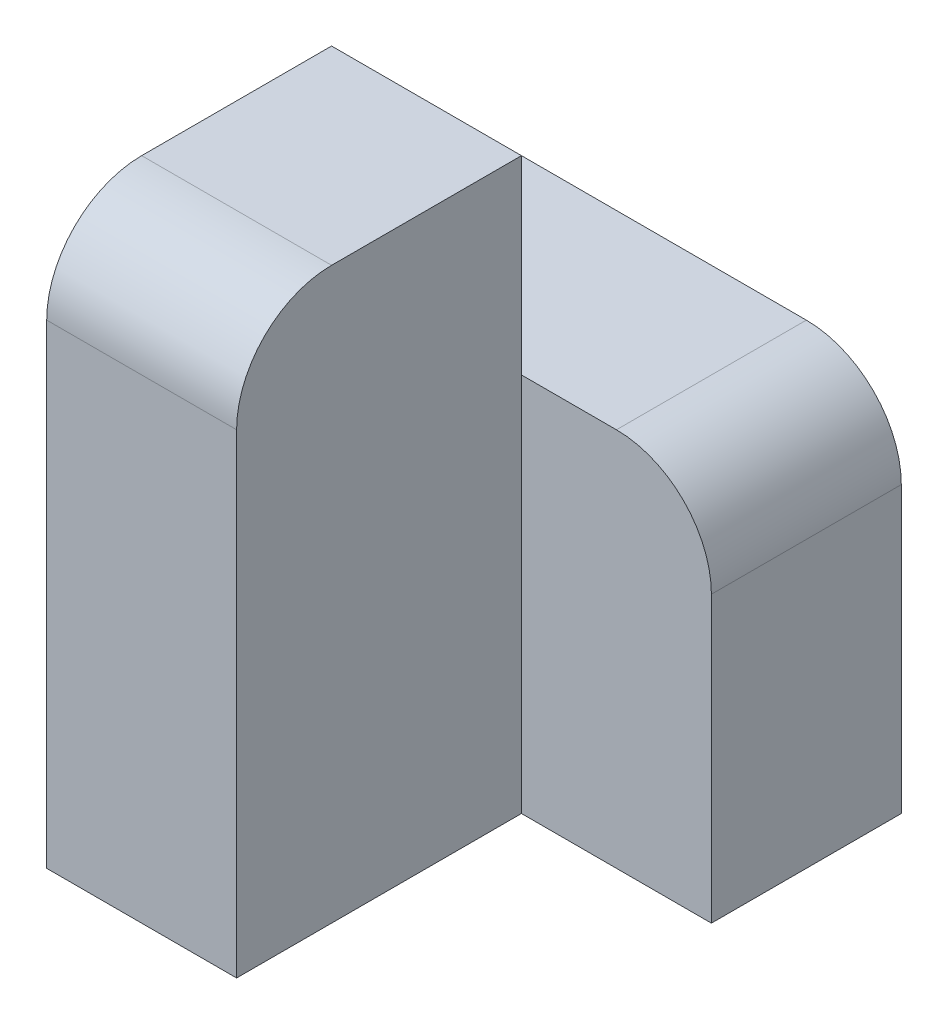
SolidWorks part; units mm, degrees
ref_plane "Front Plane" through (0, 0, 0) normal (0, 0, 1) x (1, 0, 0)
ref_plane "Top Plane" through (0, 0, 0) normal (0, 1, 0) x (1, 0, 0)
ref_plane "Right Plane" through (0, 0, 0) normal (1, 0, 0) x (0, 0, -1)
sketch "Sketch1" plane through (0, 0, 0) normal (0, 0, 1) x (1, 0, 0)
  line L1 (-30, -60) -> (-10, -60)
  line L2 (-10, -60) -> (-10, 0)
  line L3 (-10, 0) -> (-30, 0)
  line L4 (-30, 0) -> (-30, -60)
  dimension "D1" = 20
  dimension "Width" = 60
extrude "Boss-Extrude1" add sketch "Sketch1" along normal blind 30
sketch "Sketch2" plane through (0, 0, 0) normal (0, 0, 1) x (1, 0, 0)
  line L1 (-30, -60) -> (10, -60)
  line L2 (10, -60) -> (10, -20)
  line L3 (10, -20) -> (-30, -20)
  line L4 (-30, -20) -> (-30, -60)
  dimension "D1" = 40
  dimension "Width" = 40
extrude "Boss-Extrude2" add sketch "Sketch2" against normal blind 20
fillet "Fillet1" radius 10 2 edges at (10, -20, -10) (-20, 0, 30)
